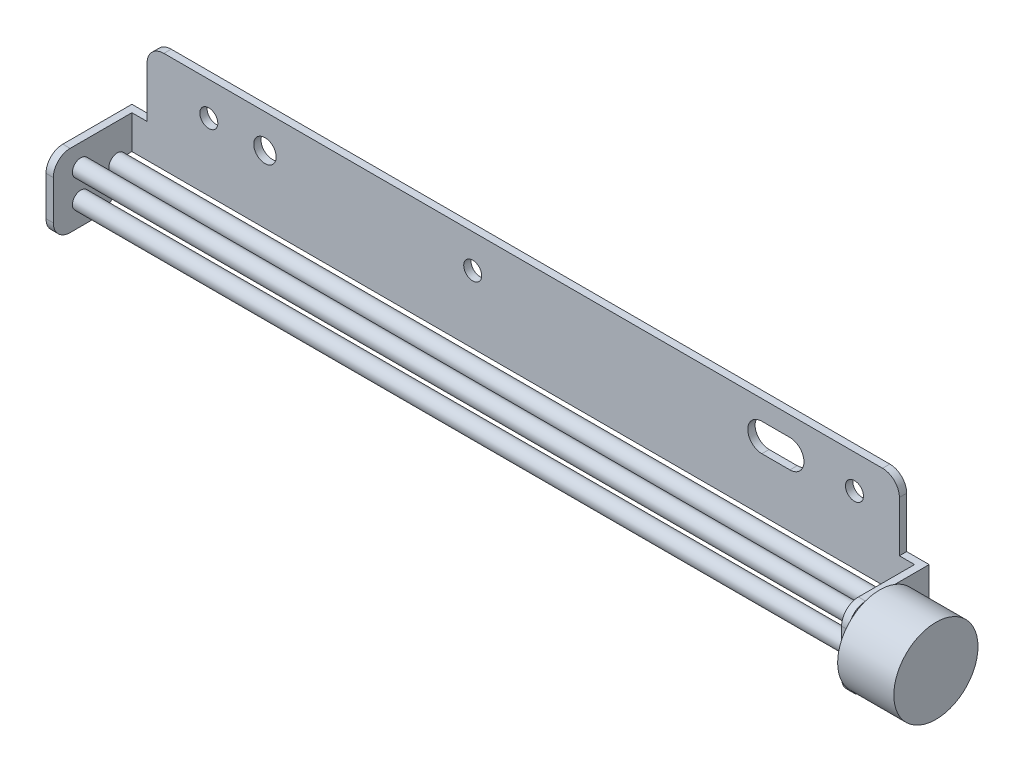
SolidWorks part; units mm, degrees
ref_plane "前视基准面" through (0, 0, 0) normal (0, 0, 1) x (1, 0, 0)
ref_plane "上视基准面" through (0, 0, 0) normal (0, 1, 0) x (1, 0, 0)
ref_plane "右视基准面" through (0, 0, 0) normal (1, 0, 0) x (0, 0, -1)
other "Configuration Table"
sketch "草图1" plane through (0, 0, 0) normal (0, 0, 1) x (1, 0, 0)
  line L0 (-71, 0) -> (0, 0)
  line L1 (0, 0) -> (71, 0)
  line L2 (71, 0) -> (71, 6)
  line L3 (71, 6) -> (67, 6)
  line L4 (67, 6) -> (67, 18)
  line L5 (67, 18) -> (-67, 18)
  line L6 (-67, 18) -> (-67, 6)
  line L7 (-67, 6) -> (-71, 6)
  line L8 (-71, 6) -> (-71, 0)
  dimension "D1" = 71
  dimension "D2" = 71
  dimension "D3" = 6
  dimension "D4" = 12
  dimension "D5" = 4
  dimension "D6" = 4
  dimension "D7" = 12
extrude "凸台-拉伸1" add sketch "草图1" against normal blind 1.3
fillet "圆角1" radius 3 2 edges at (67, 18, -0.65) (-67, 18, -0.65)
sketch "草图2" plane through (0, 0, 0) normal (0, 0, 1) x (1, 0, 0)
  line L0 (0, 0) -> (0, 18) construction
  line L1 (64, 18) -> (-64, 18) construction
  line L2 (-69.7, 6) -> (-69.7, 0) construction
  line L3 (-67, 6) -> (-71, 6) construction
  line L4 (-71, 0) -> (71, 0) construction
  line L5 (-71, 6) -> (-71, 0) construction
  line L7 (-71, 6) -> (-69.7, 6)
  line L8 (-71, 6) -> (-71, 0)
  line L9 (-71, 0) -> (-69.7, 0)
  line L10 (-69.7, 6) -> (-69.7, 0)
  dimension "D1" = 1.3
extrude "凸台-拉伸2" add sketch "草图2" along normal blind 14
fillet "圆角2" radius 3 1 edges at (-70.35, 6, 14)
sketch "草图3" plane through (0, 0, 0) normal (0, -1, 0) x (1, 0, 0)
  line L0 (-71, 6.35) -> (-69.7, 6.35) construction
  line L1 (-71, -1.3) -> (-71, 14) construction
  line L2 (-69.7, 14) -> (-69.7, 0) construction
  line L4 (-71, 14) -> (-69.7, 14)
  line L5 (-71, 14) -> (-71, 6.35)
  line L6 (-71, 6.35) -> (-69.7, 6.35)
  line L7 (-69.7, 14) -> (-69.7, 6.35)
extrude "凸台-拉伸3" add sketch "草图3" along normal blind 7
sketch "草图4" plane through (0, 0, 0) normal (0, -1, 0) x (1, 0, 0)
  line L0 (-71, 2) -> (-69.7, 2) construction
  line L1 (-71, -1.3) -> (-71, 6.35) construction
  line L2 (-69.7, 6.35) -> (-69.7, 0) construction
  line L3 (-69.7, 0) -> (71, 0) construction
  line L5 (-71, 6.35) -> (-69.7, 6.35)
  line L6 (-71, 6.35) -> (-71, 2)
  line L7 (-71, 2) -> (-69.7, 2)
  line L8 (-69.7, 6.35) -> (-69.7, 2)
  dimension "D1" = 2
extrude "凸台-拉伸4" add sketch "草图4" along normal blind 7
fillet "圆角3" radius 3 1 edges at (-70.35, -7, 14)
fillet "圆角4" radius 5 1 edges at (-70.35, -7, 2)
sketch "草图6" plane through (0, 0, 0) normal (0, 0, 1) x (1, 0, 0)
  line L0 (69.7, 6) -> (69.7, 0) construction
  line L1 (71, 6) -> (67, 6) construction
  line L2 (-69.7, 0) -> (71, 0) construction
  line L3 (71, 0) -> (71, 6) construction
  line L5 (69.7, 6) -> (71, 6)
  line L6 (69.7, 6) -> (69.7, 0)
  line L7 (69.7, 0) -> (71, 0)
  line L8 (71, 6) -> (71, 0)
  dimension "D1" = 1.3
extrude "凸台-拉伸5" add sketch "草图6" along normal blind 13
sketch "草图7" plane through (0, 0, 0) normal (0, -1, 0) x (1, 0, 0)
  line L0 (71, -1.3) -> (71, 13) construction
  line L1 (69.7, 13) -> (71, 13)
  line L2 (69.7, 13) -> (69.7, 0)
  line L3 (69.7, 0) -> (71, 0)
  line L4 (71, 13) -> (71, 0)
extrude "凸台-拉伸6" add sketch "草图7" along normal blind 8
fillet "圆角5" radius 3 2 edges at (70.35, -8, 13) (70.35, 6, 13)
fillet "圆角6" radius 5 1 edges at (70.35, -8, 0)
sketch "草图8" plane through (0, 0, 0) normal (0, 0, 1) x (1, 0, 0)
  line L0 (-67, 12) -> (67, 12) construction
  line L1 (-67, 15) -> (-67, 6) construction
  line L2 (67, 6) -> (67, 15) construction
  line L3 (-56, 18) -> (-56, 0) construction
  line L4 (64, 18) -> (-64, 18) construction
  line L5 (-69.7, 0) -> (69.7, 0) construction
  line L6 (-46, 18) -> (-46, 0) construction
  line L7 (-9, 18) -> (-9, 0) construction
  line L8 (45, 18) -> (45, 0) construction
  line L9 (59, 18) -> (59, 0) construction
  line L10 (42.5, 12) -> (47.5, 12) construction
  line L11 (42.5, 14.5) -> (47.5, 14.5)
  line L12 (42.5, 9.5) -> (47.5, 9.5)
  circle A0 centre (-56, 12) radius 1.6
  circle A1 centre (-46, 12) radius 2
  circle A2 centre (-9, 12) radius 1.6
  circle A3 centre (59, 12) radius 1.6
  arc A4 (42.5, 14.5) -> (42.5, 9.5) centre (42.5, 12) ccw
  arc A5 (47.5, 9.5) -> (47.5, 14.5) centre (47.5, 12) ccw
  point P20 (-56, 12)
  point P21 (-46, 12)
  point P22 (-9, 12)
  point P23 (45, 12)
  point P24 (59, 12)
  point P35 (45, 12)
  point P40 (0, 0)
  point P42 (-9, 12)
  dimension "D7" = 3.2
  dimension "D8" = 4
  dimension "D1" = 6
  dimension "D2" = 11
  dimension "D3" = 10
  dimension "D4" = 37
  dimension "D5" = 54
  dimension "D6" = 14
  dimension "D9" = 5
  dimension "D10" = 5
extrude "切除-拉伸1" cut sketch "草图8" against normal blind 8
sketch "草图9" plane through (71, 0, 0) normal (1, 0, 0) x (0, 0, -1)
  line L0 (-13, -1) -> (0, -1) construction
  line L1 (-13, -5) -> (-13, 3) construction
  line L2 (0, -3) -> (0, 0) construction
  line L3 (-7.5, -8) -> (-7.5, 6) construction
  line L4 (-5, -8) -> (-10, -8) construction
  line L5 (1.3, 6) -> (-10, 6) construction
  circle A0 centre (-7.5, -1) radius 7.5
  point P12 (-7.5, -1)
  dimension "D1" = 15
extrude "凸台-拉伸7" add sketch "草图9" along normal blind 10
sketch "草图10" plane through (69.7, 0, 0) normal (-1, 0, 0) x (0, 0, 1)
  line L0 (0, 0) -> (13, 0) construction
  line L1 (13, 3) -> (13, -5) construction
  line L2 (6, 6) -> (6, -8) construction
  line L6 (10, 6) -> (0, 6) construction
  line L7 (10, -8) -> (5, -8) construction
  line L8 (0, -2.5) -> (13, -2.5) construction
  line L9 (0, -3) -> (0, 0) construction
  line L10 (3, 6) -> (3, -7.5826) construction
  line L11 (9.5, 6) -> (9.5, -8) construction
  line L12 (0, 2.5) -> (13, 2.5) construction
  line L13 (0, 6) -> (0, 0) construction
  arc A0 (0, -3) -> (5, -8) centre (5, -3) ccw construction
  circle A3 centre (9.5, 2.5) radius 1.5
  circle A5 centre (9.5, -2.5) radius 1.5
  circle A7 centre (3, 0) radius 1.5
  point P27 (6, 2.5)
  point P28 (3, -2.5)
  point P29 (9.5, -2.5)
  point P30 (6, -2.5)
  point P31 (3, 2.5)
  point P32 (9.5, 2.5)
  point P33 (3, 0)
  dimension "D6" = 3
  dimension "D1" = 7
  dimension "D2" = 2.5
  dimension "D3" = 3.5
  dimension "D4" = 3
  dimension "D5" = 2.5
extrude "凸台-拉伸10" add sketch "草图10" along normal blind 139
cosmetic thread "装饰螺纹线1" parameters "D2"=2.459
